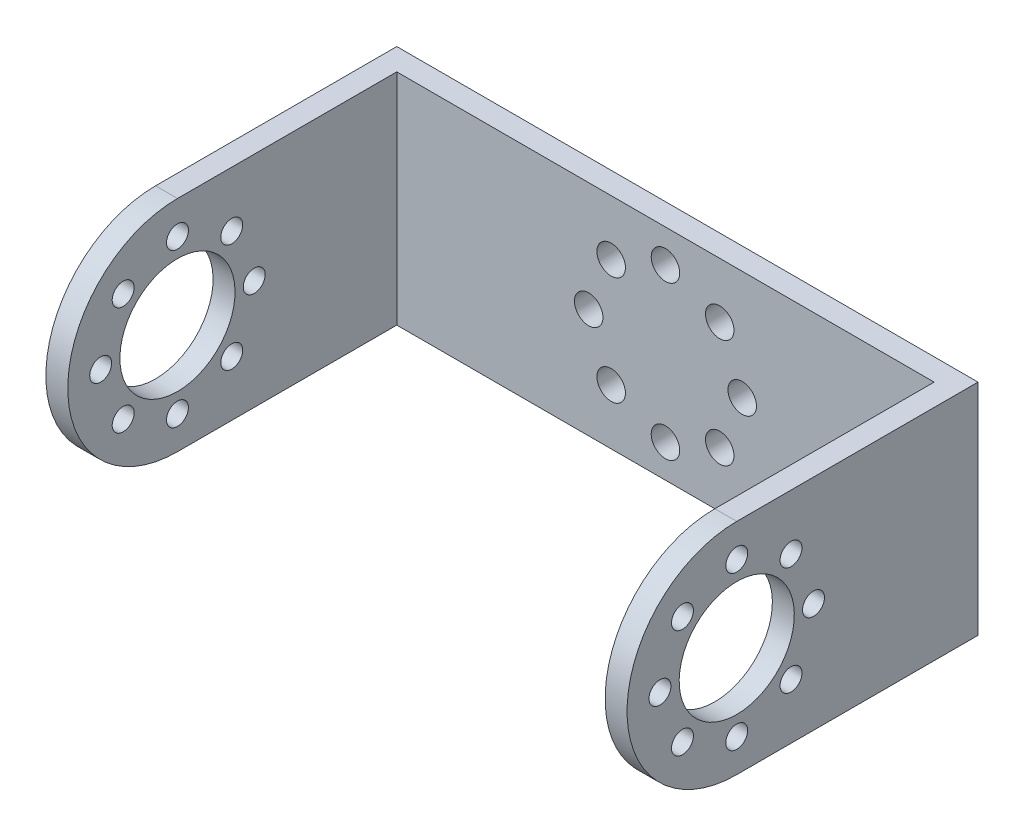
SolidWorks part; units mm, degrees
ref_plane "前基準面" through (0, 0, 0) normal (0, 0, 1) x (1, 0, 0)
ref_plane "上基準面" through (0, 0, 0) normal (0, 1, 0) x (1, 0, 0)
ref_plane "右基準面" through (0, 0, 0) normal (1, 0, 0) x (0, 0, -1)
sketch "草圖1" plane through (0, 0, 0) normal (0, 0, 1) x (1, 0, 0)
  line L1 (-26.5, 10) -> (26.5, 10)
  line L2 (-26.5, 10) -> (-26.5, -10)
  line L3 (-26.5, -10) -> (26.5, -10)
  line L4 (26.5, 10) -> (26.5, -10)
  line L5 (-26.5, 10) -> (26.5, -10) construction
  line L6 (-26.5, -10) -> (26.5, 10) construction
  point P0 (0, 0)
  dimension "D1" = 20
  dimension "D2" = 53
extrude "填料-伸長1" add sketch "草圖1" along normal blind 2
sketch "草圖2" plane through (0, 0, 2) normal (0, 0, 1) x (1, 0, 0)
  line L0 (-26.5, -10) -> (26.5, -10) construction
  line L1 (-26.5, 10) -> (-24.5, 10)
  line L2 (-26.5, 10) -> (-26.5, -10)
  line L3 (-26.5, -10) -> (-24.5, -10)
  line L4 (-24.5, 10) -> (-24.5, -10)
  dimension "D1" = 2
extrude "填料-伸長2" add sketch "草圖2" along normal blind 30
sketch "草圖3" plane through (-24.5, 0, 0) normal (1, 0, 0) x (0, 0, -1)
  line L0 (-22, 10) -> (-22, -10) construction
  line L1 (-32, 10) -> (-2, 10) construction
  line L2 (-32, -10) -> (-2, -10) construction
  line L3 (-32, -10) -> (-32, 10) construction
  arc A0 (-22, -10) -> (-22, 10) centre (-22, 0) cw
  line M3 (-2, 10) -> (-32, 10)
  line M4 (-32, 10) -> (-32, -10)
  line M5 (-32, -10) -> (-2, -10)
  dimension "D1" = 10
extrude "除料-伸長1" cut sketch "草圖3" against normal blind 30 and the other way through all contours A0 M4 M3 | A0 M5 M4
sketch "草圖4" plane through (-26.5, 0, 0) normal (-1, 0, 0) x (0, 0, 1)
  line L0 (0, 0) -> (32, 0) construction
  line L1 (0, 10) -> (0, -10) construction
  line L2 (22, 0) -> (29, 0) construction
  arc A0 (22, -10) -> (22, 10) centre (22, 0) ccw construction
  circle A1 centre (29, 0) radius 1
  circle A2 centre (26.9497, -4.9497) radius 1
  circle A3 centre (22, -7) radius 1
  circle A4 centre (17.0503, -4.9497) radius 1
  circle A5 centre (15, 0) radius 1
  circle A6 centre (17.0503, 4.9497) radius 1
  circle A7 centre (22, 7) radius 1
  circle A8 centre (26.9497, 4.9497) radius 1
  circle A9 centre (22, 0) radius 5.25
  point P7 (22, 0)
  dimension "D2" = 2
  dimension "D5" = 10.5
  dimension "D1" = 10
  dimension "D3" = 7
  dimension "D4" = 8
extrude "除料-伸長2" cut sketch "草圖4" against normal up to next (2 mm away)
mirror "鏡射1" about plane through (0, 0, 0) normal (1, 0, 0) of "除料-伸長2", "除料-伸長1", "填料-伸長2"
sketch "草圖5" plane through (0, 0, 0) normal (0, 0, -1) x (-1, 0, 0)
  line L0 (-26.5, 0) -> (26.5, 0) construction
  line L1 (-26.5, -10) -> (-26.5, 10) construction
  line L2 (26.5, 10) -> (26.5, -10) construction
  circle A0 centre (-7, 0) radius 1.3
  circle A1 centre (-4.9497, 4.9497) radius 1.3
  circle A2 centre (0, 7) radius 1.3
  circle A3 centre (4.9497, 4.9497) radius 1.3
  circle A4 centre (7, 0) radius 1.3
  circle A5 centre (4.9497, -4.9497) radius 1.3
  circle A6 centre (0, -7) radius 1.3
  circle A7 centre (-4.9497, -4.9497) radius 1.3
  point P6 (0, 0)
  point P26 (0, 0)
  dimension "D1" = 2.6
  dimension "D2" = 7
  dimension "D3" = 8
extrude "除料-伸長3" cut sketch "草圖5" against normal through all
